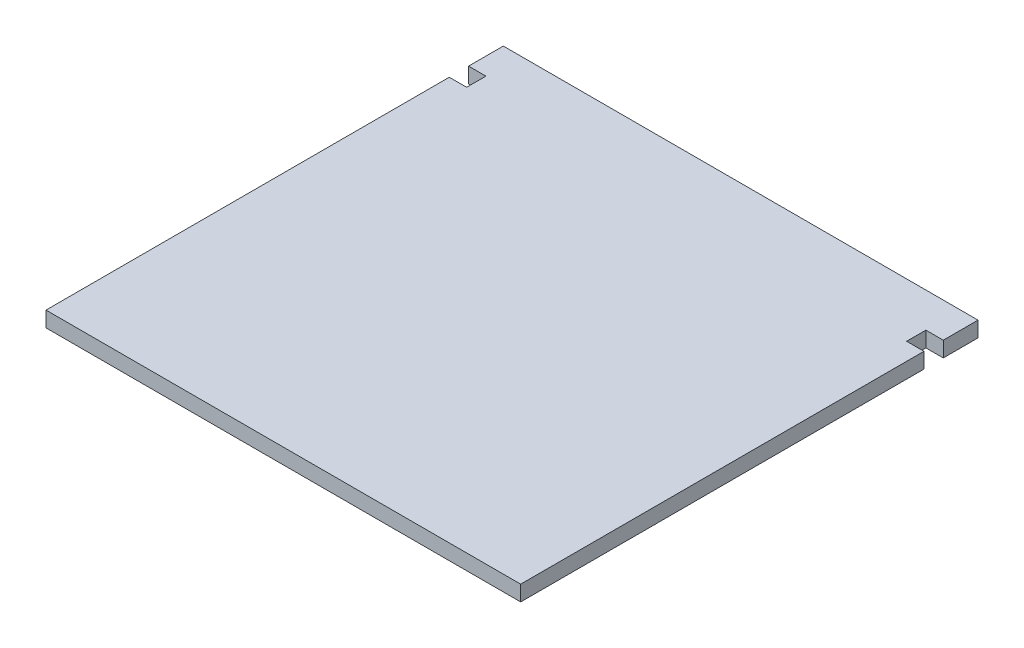
SolidWorks part; units mm, degrees
ref_plane "Спереди" through (0, 0, 0) normal (0, 0, 1) x (1, 0, 0)
ref_plane "Сверху" through (0, 0, 0) normal (0, 1, 0) x (1, 0, 0)
ref_plane "Справа" through (0, 0, 0) normal (1, 0, 0) x (0, 0, -1)
sketch "Эскиз1" plane through (0, 0, 0) normal (0, 1, 0) x (1, 0, 0)
  line L0 (0, 0) -> (0, 125.7883) construction
  line L1 (61.5, 0) -> (-61.5, 0)
  line L2 (-61.5, 0) -> (-61.5, 104.5)
  line L3 (-61.5, 104.5) -> (-57, 104.5)
  line L4 (-57, 104.5) -> (-57, 109.5)
  line L5 (-57, 109.5) -> (-61.5, 109.5)
  line L6 (-61.5, 109.5) -> (-61.5, 118.5)
  line L7 (-61.5, 118.5) -> (61.5, 118.5)
  line L8 (61.5, 109.5) -> (61.5, 118.5)
  line L9 (57, 109.5) -> (61.5, 109.5)
  line L10 (57, 104.5) -> (57, 109.5)
  line L11 (61.5, 104.5) -> (57, 104.5)
  line L12 (61.5, 0) -> (61.5, 104.5)
  point P11 (0, 118.5)
  dimension "D1" = 123
  dimension "D2" = 118.5
  dimension "D3" = 4.5
  dimension "D4" = 9
  dimension "D5" = 5
extrude "Бобышка-Вытянуть1" add sketch "Эскиз1" along normal blind 4
